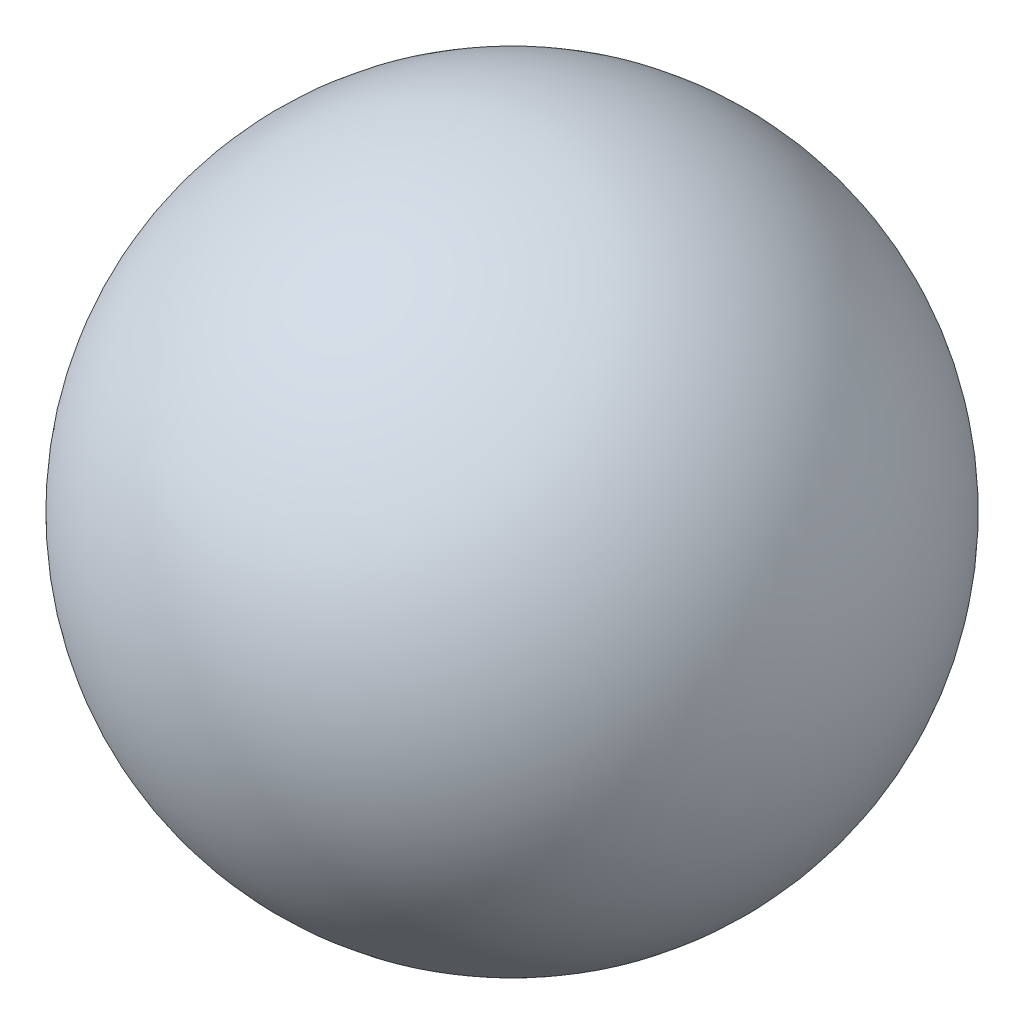
SolidWorks part; units mm, degrees
ref_plane "Front Plane" through (0, 0, 0) normal (0, 0, 1) x (1, 0, 0)
ref_plane "Top Plane" through (0, 0, 0) normal (0, 1, 0) x (1, 0, 0)
ref_plane "Right Plane" through (0, 0, 0) normal (1, 0, 0) x (0, 0, -1)
sketch "Sketch1" plane through (0, 0, 0) normal (0, 0, 1) x (1, 0, 0)
  line L0 (0, 21.336) -> (0, -21.336)
  arc A0 (0, -21.336) -> (0, 21.336) centre (0, 0) ccw
  dimension "D1" = 42.672
ref_axis "Axis1" through (0, 23.4696, 0) along (0, -1, 0)
revolve "Revolve2" add sketch "Sketch1" angle 360 about axis through (0, 23.4696, 0) along (0, -1, 0)
